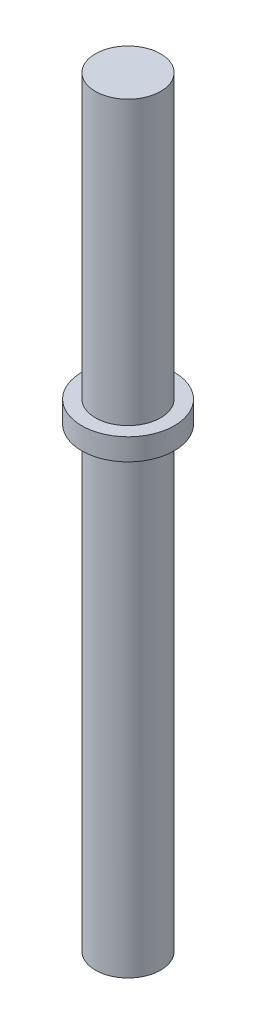
SolidWorks part; units mm, degrees
ref_plane "Front Plane" through (0, 0, 0) normal (0, 0, 1) x (1, 0, 0)
ref_plane "Top Plane" through (0, 0, 0) normal (0, 1, 0) x (1, 0, 0)
ref_plane "Right Plane" through (0, 0, 0) normal (1, 0, 0) x (0, 0, -1)
sketch "Sketch1" plane through (0, 0, 0) normal (0, 1, 0) x (1, 0, 0)
  circle A0 centre (0, 0) radius 1.5
  dimension "D1" = 3
extrude "Boss-Extrude1" add sketch "Sketch1" along normal blind 35
sketch "Sketch2" plane through (0, 0, 0) normal (1, 0, 0) x (0, 0, -1)
  line L0 (0, 35) -> (0, 0) construction
  line L1 (1.5, 35) -> (-1.5, 35) construction
  line L2 (0, 17.5) -> (0, 21) construction
  dimension "D1" = 3.5
ref_plane "Plane1" through (0, 21, 0) normal (0, -1, 0) x (-1, 0, 0)
sketch "Sketch4" plane through (0, 21, 0) normal (0, -1, 0) x (-1, 0, 0)
  circle A0 centre (0, 0) radius 2.1298
extrude "Boss-Extrude2" add sketch "Sketch4" against normal blind 1
